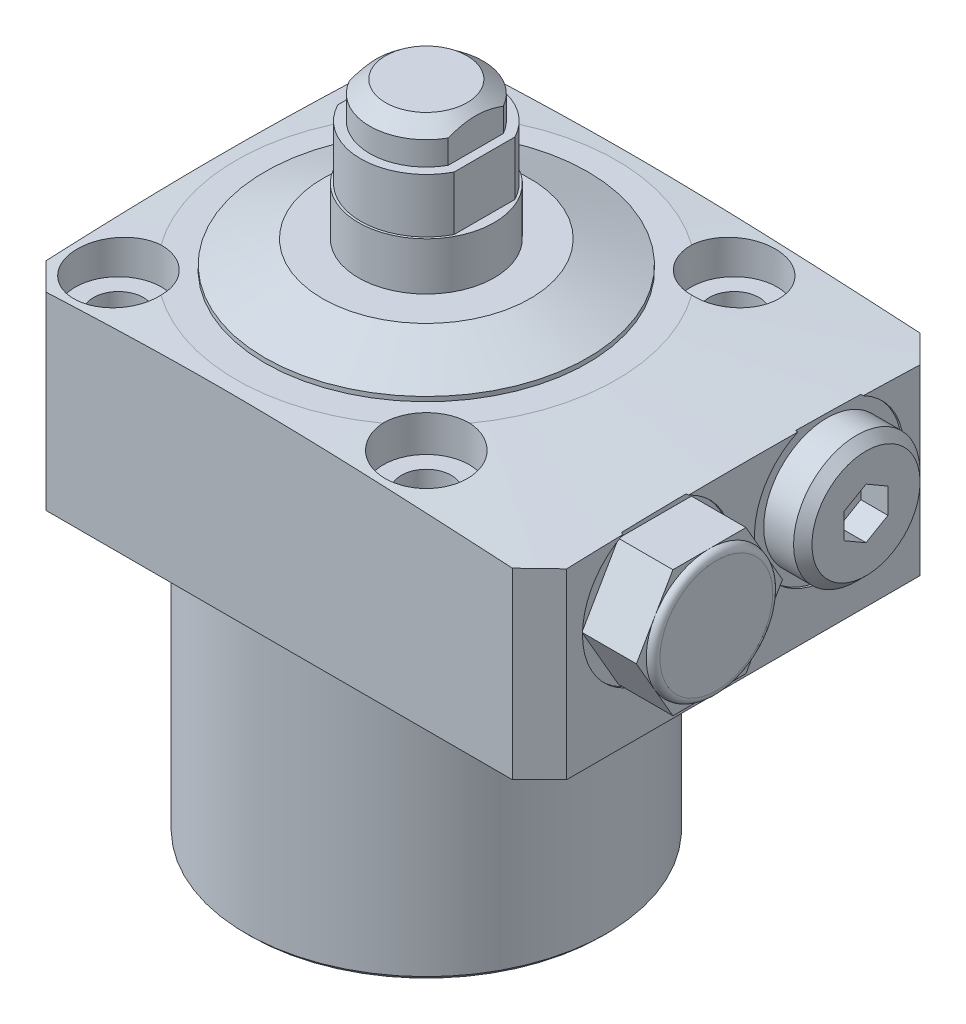
SolidWorks part; units mm, degrees
material "Alloy Steel"
ref_plane "Front Plane" through (0, 0, 0) normal (0, 0, 1) x (1, 0, 0)
ref_plane "Top Plane" through (0, 0, 0) normal (0, 1, 0) x (1, 0, 0)
ref_plane "Right Plane" through (0, 0, 0) normal (1, 0, 0) x (0, 0, -1)
sketch "Sketch1" plane through (0, 0, 0) normal (0, 0, 1) x (1, 0, 0)
  line L0 (0, 0) -> (0, -9.6761) construction
  line L1 (-19.925, 0) -> (-50, 0)
  line L2 (-50, 0) -> (-50, 19.4721)
  line L8 (-19.925, -32.5) -> (-19.925, 0)
  line L9 (-50, 19.4721) -> (-21, 21.5)
  line L10 (-21, 21.5) -> (0, 21.5)
  line L11 (0, 21.5) -> (0, -32.5)
  line L13 (-19.925, -32.5) -> (0, -32.5)
  dimension "D2" = 32.5
  dimension "D3" = 50
  dimension "D7" = 54
  dimension "D8" = 4
  dimension "D9" = 42
  dimension "D10" = 39.85
revolve "Revolve1" add sketch "Sketch1" angle 360 about L0
sketch "Sketch2" plane through (0, 21.5, 0) normal (0, 1, 0) x (1, 0, 0)
  line L0 (0, 0) -> (0, 57.0347) construction
  line L1 (-22.5, 22.5) -> (35, 22.5)
  line L2 (-22.5, 22.5) -> (-22.5, -22.5)
  line L3 (-22.5, -22.5) -> (35, -22.5)
  line L4 (35, 22.5) -> (35, -22.5)
  line L5 (0, 0) -> (-71.4399, 0) construction
  dimension "D1" = 45
  dimension "D2" = 22.5
  dimension "D3" = 57.5
extrude "Cut-Extrude1" cut sketch "Sketch2" against normal through all flip side to cut
chamfer "Chamfer2" distance 3 angle 45 4 edges at (-22.5, 10.3717, -22.5) (35, 10.0295, -22.5) (35, 10.0295, 22.5) (-22.5, 10.3717, 22.5)
sketch "Sketch4" plane through (0, 0, 0) normal (0, 0, 1) x (1, 0, 0)
  line L0 (0, 0) -> (0, 85.9979) construction
  line L1 (0, 39.75) -> (-6.25, 39.75)
  line L2 (-6.25, 39.75) -> (-6.25, 35.762)
  line L3 (-6.25, 35.762) -> (-7.25, 35.762)
  line L4 (-7.25, 35.762) -> (-7.25, 29.782)
  line L5 (-7.25, 29.782) -> (-7.5, 29.782)
  line L6 (-7.5, 29.782) -> (-7.5, 21.5)
  line L7 (21, 21.5) -> (-21, 21.5) construction
  line L8 (-7.5, 21.5) -> (0, 21.5)
  line L9 (0, 21.5) -> (0, 39.75)
  line L12 (32, 0) -> (-19.5, 0) construction
  dimension "D1" = 39.75
  dimension "D2" = 3.988
  dimension "D3" = 12.5
  dimension "D4" = 15
  dimension "D5" = 14.5
  dimension "D6" = 9.968
revolve "Revolve2" add sketch "Sketch4" angle 360 about L0
chamfer "Chamfer1" distance 1.3715 angle 51.98 1 edges at (0, 39.75, -6.25)
sketch "Sketch5" plane through (0, 0, 0) normal (0, 0, 1) x (1, 0, 0)
  line L0 (7.25, 35.762) -> (-7.25, 35.762) construction
  line L1 (-5.46, 35.762) -> (-7.25, 35.762)
  line L2 (-5.46, 35.762) -> (-5.46, 39.75)
  line L3 (-5.46, 39.75) -> (-7.25, 39.75)
  line L4 (-7.25, 35.762) -> (-7.25, 39.75)
  line L5 (4.4959, 39.75) -> (-4.4959, 39.75) construction
  line L6 (-7.25, 35.762) -> (-7.25, 29.782) construction
  line L7 (0, 0) -> (0, 109.405) construction
  line L8 (7.25, 35.762) -> (7.25, 39.75)
  line L9 (5.46, 39.75) -> (7.25, 39.75)
  line L10 (5.46, 35.762) -> (5.46, 39.75)
  line L11 (5.46, 35.762) -> (7.25, 35.762)
  dimension "D1" = 10.92
extrude "Cut-Extrude2" cut sketch "Sketch5" against normal through all and the other way through all
sketch "Sketch6" plane through (0, 0, 0) normal (0, 0, 1) x (1, 0, 0)
  line L0 (7.25, 35.762) -> (-7.25, 35.762) construction
  line L1 (-6.425, 35.762) -> (-7.5, 35.762)
  line L2 (-6.425, 35.762) -> (-6.425, 29.782)
  line L3 (-6.425, 29.782) -> (-7.5, 29.782)
  line L4 (-7.5, 35.762) -> (-7.5, 29.782)
  line L5 (0, 0) -> (0, 83.5625) construction
  line L6 (7.5, 35.762) -> (7.5, 29.782)
  line L7 (6.425, 29.782) -> (7.5, 29.782)
  line L8 (6.425, 35.762) -> (6.425, 29.782)
  line L9 (6.425, 35.762) -> (7.5, 35.762)
  dimension "D1" = 12.85
extrude "Cut-Extrude3" cut sketch "Sketch6" against normal through all and the other way through all
sketch "Sketch10" plane through (0, 21.5, 0) normal (0, 1, 0) x (1, 0, 0)
  line L0 (0, 0) -> (0, 37.6461) construction
  line L1 (0, 0) -> (33.5022, 0) construction
  circle A0 centre (-17, 17) radius 4.75
  dimension "D1" = 9.5
  dimension "D2" = 17
  dimension "D3" = 17
extrude "Cut-Extrude4" cut sketch "Sketch10" against normal offset from surface (4 mm away) 17.5 up to face at (0, 0, 19.925)
hole_wizard "Ø5.5 (5.5) Diameter Hole1" positions "3DSketch1" profile "Sketch11" hole size "Ø5.5" standard "Ansi Metric" end condition through all
sketch3d "3DSketch1"
  circle A0 centre (-17, 17.5, -17) radius 4.75 construction
  point P0 (-17, 17.5, -17)
  point P6 (-17, 22.25, -17)
sketch "Sketch11" plane through (-17, 17.5, -17) normal (1, 0, 0) x (0, 0, 1)
  line L0 (0, 0) -> (0, 50)
  line L1 (0, 50) -> (2.75, 50)
  line L2 (2.75, 50) -> (2.75, 0)
  line L5 (2.75, 0) -> (0, 0)
  line L11 (0, -6.35) -> (0, 107.95) construction
  dimension "Thru Hole Dia." = 5.5
  dimension "Thru Hole Depth" = 50
pattern_circular "CirPattern1" count 4 over 360 about axis through (0, 0, 0) along (0, 1, 0) of "Ø5.5 (5.5) Diameter Hole1", "Cut-Extrude4"
ref_plane "Plane1" through (0, 0, -9.5) normal (0, 0, 1) x (1, 0, 0)
sketch "Sketch12" plane through (0, 0, -9.5) normal (0, 0, 1) x (1, 0, 0)
  line L0 (17.9573, 13) -> (55.5469, 13) construction
  line L2 (35, 21.255) -> (34.75, 21.255)
  line L4 (34.75, 21.255) -> (34.75, 17.953)
  line L5 (34.75, 17.953) -> (34.2166, 17.4196)
  line L6 (34.2166, 17.4196) -> (24.1836, 17.4196)
  line L7 (24.1836, 17.4196) -> (21.528, 13)
  line L8 (21.528, 13) -> (35, 13)
  line L9 (35, 13) -> (35, 21.255)
  line L10 (35, 20.1668) -> (35, 0) construction
  line L11 (-19.925, -32.5) -> (19.925, -32.5) construction
  dimension "D1" = 45.5
  dimension "D2" = 16.51
  dimension "D3" = 0.25
  dimension "D4" = 8.8392
  dimension "D5" = 59
  dimension "D6" = 10.5664
  dimension "D7" = 45
  dimension "D8" = 0.5334
revolve "Cut-Revolve2" cut sketch "Sketch12" angle 360 about L0
sketch "Sketch13" plane through (0, 0, -9.5) normal (0, 0, 1) x (1, 0, 0)
  line L0 (10.4663, 13) -> (36.2703, 13) construction
  line L1 (34.2166, 13) -> (24.1836, 13) construction
  line L3 (34.75, 19.985) -> (38.045, 19.985)
  line L4 (34.75, 4.745) -> (34.75, 20.5019) construction
  line L5 (38.045, 19.985) -> (39.06, 18.97)
  line L6 (39.06, 18.97) -> (39.06, 13)
  line L7 (39.06, 13) -> (34.75, 13)
  line L8 (34.75, 13) -> (34.75, 19.985)
  dimension "D1" = 4.31
  dimension "D2" = 13.97
  dimension "D3" = 45
  dimension "D4" = 1.015
revolve "Revolve3" add sketch "Sketch13" angle 360 about L0
sketch "Sketch14" plane through (39.06, 0, 0) normal (1, 0, 0) x (0, 0, -1)
  line L1 (11.9255, 11.5996) -> (11.9255, 14.4004)
  line L2 (11.9255, 14.4004) -> (9.5, 15.8007)
  line L3 (9.5, 15.8007) -> (7.0745, 14.4004)
  line L4 (7.0745, 14.4004) -> (7.0745, 11.5996)
  line L5 (7.0745, 11.5996) -> (9.5, 10.1993)
  line L6 (9.5, 10.1993) -> (11.9255, 11.5996)
  circle A0 centre (9.5, 13) radius 2.4255 construction
  dimension "D1" = 4.851
extrude "Cut-Extrude5" cut sketch "Sketch14" against normal blind 3
sketch "Sketch16" plane through (9.5, 0, -9.5) normal (0, 0, -1) x (-1, 0, 0)
  line L0 (-17.5, -1.224) -> (-17.5, -24.6754) construction
  line L1 (-17.5, 13.5022) -> (-20, 12)
  line L2 (-20, 12) -> (-20, 2.875)
  line L3 (-20, 2.875) -> (-20.625, 2.25)
  line L4 (-20.625, 2.25) -> (-22.5, 2.25)
  line L5 (-22.5, 2.25) -> (-22.5, 0)
  line L7 (-22.5, 0) -> (-17.5, 0)
  line L8 (-17.5, 0) -> (-17.5, 13.5022)
  line L9 (9.5, -32.5) -> (9.5, 0) construction
  line L10 (29, 0) -> (-22.5, 0) construction
  dimension "D1" = 27
  dimension "D2" = 5
  dimension "D3" = 59
  dimension "D4" = 10
  dimension "D5" = 2.25
  dimension "D6" = 45
  dimension "D7" = 0.625
  dimension "D8" = 9.75
revolve "Cut-Revolve4" cut sketch "Sketch16" angle 360 about L0
pattern_linear "LPattern1" count 2 spacing 19 along (0, 0, 1) of "Cut-Extrude5", "Cut-Revolve2", "Cut-Revolve4"
sketch "Sketch18" plane through (-9.5, 0, -9.5) normal (0, 0, 1) x (1, 0, 0)
  line L0 (36.5, -2.5857) -> (36.5, -21.6782) construction
  line L3 (31.5, 2.25) -> (41.5, 2.25) construction
  line L4 (36.5, 2.875) -> (36.5, 8.5804) construction
  circle A0 centre (33.001, 0.75) radius 1.5
  dimension "D1" = 3
  dimension "D2" = 1.5
  dimension "D3" = 6.998
revolve "Revolve4" add sketch "Sketch18" angle 360 about L0
pattern_linear "LPattern2" count 2 spacing 19 along (0, 0, 1) of bodies 124
chamfer "Chamfer3" distance 0.5 angle 45 1 edges at (0, -32.5, 19.925)
fillet "Fillet1" radius 0.5 1 edges at (0, 0, 19.925)
ref_axis "Axis1" through (0, 29.782, 0) along (0, -1, 0)
sketch "Sketch19" plane through (0, 0, 0) normal (0, 0, 1) x (1, 0, 0)
  line L0 (7.5, 21.5) -> (17.82, 21.5)
  line L1 (21, 21.5) -> (17.0566, 21.5) construction
  line L2 (17.82, 21.5) -> (17.82, 22)
  line L3 (17.82, 22) -> (11.4734, 24.5)
  line L4 (11.4734, 24.5) -> (7.5, 24.5)
  line L5 (7.5, 21.5) -> (7.5, 29.782) construction
  line L6 (7.5, 24.5) -> (7.5, 21.5)
  line L7 (0, 29.782) -> (0, 21.5) construction
  dimension "D1" = 17.82
  dimension "D2" = 21.5
  dimension "D3" = 0.5
  dimension "D4" = 3
revolve "Revolve5" add sketch "Sketch19" angle 360 about axis through (0, 29.782, 0) along (0, -1, 0)
sketch "Sketch20" plane through (34.75, 0, 0) normal (1, 0, 0) x (0, 0, -1)
  line L1 (-1.4344, 13) -> (-5.4672, 19.985)
  line L2 (-5.4672, 19.985) -> (-13.5328, 19.985)
  line L3 (-13.5328, 19.985) -> (-17.5656, 13)
  line L4 (-17.5656, 13) -> (-13.5328, 6.015)
  line L5 (-13.5328, 6.015) -> (-5.4672, 6.015)
  line L6 (-5.4672, 6.015) -> (-1.4344, 13)
  circle A0 centre (-9.5, 13) radius 6.985 construction
  arc A1 (-13.2215, 20.3686) -> (-6.0552, 20.5019) centre (-9.5, 13) ccw
  arc A2 (-13.2215, 20.3686) -> (-6.0552, 20.5019) centre (-9.5, 13) ccw
  spline S1 degree 3 poles (847.6004, -3831.5532) (161.3283, 3919.1103) (-267.8998, -3866.713) (-953.1501, 3822.1882) knots -110.194518 -110.194518 -110.194518 -110.194518 123.34555 123.34555 123.34555 123.34555 only from (-6.0552, 20.5019) to (-13.2215, 20.3686)
  spline S2 degree 3 poles (-6.0552, 20.5019) (-8.4442, 20.4732) (-10.833, 20.428) (-13.2215, 20.3686) knots 0 0 0 0 1 1 1 1
  dimension "D2" = 13.97
  dimension "D1" = 0
extrude "Boss-Extrude2" add sketch "Sketch20" along normal blind 6.78 contours L3 L4 L5 L6 L1 L2
ref_plane "Plane2" through (0, 0, 9.5) normal (0, 0, -1) x (-1, 0, 0)
sketch "Sketch21" plane through (0, 0, 9.5) normal (0, 0, -1) x (-1, 0, 0)
  line L0 (-41.53, 19.985) -> (-41.53, 13) construction
  line L1 (-40.768, 22.9076) -> (-43.889, 22.9076)
  line L2 (-40.768, 22.9076) -> (-40.768, 19.985)
  line L3 (-41.53, 19.223) -> (-43.889, 19.223)
  line L4 (-43.889, 22.9076) -> (-43.889, 19.223)
  line L5 (-41.53, 19.985) -> (-34.75, 19.985) construction
  arc A0 (-40.768, 19.985) -> (-41.53, 19.223) centre (-40.768, 19.223) ccw
  dimension "D1" = 0.762
  dimension "D2" = 0.762
revolve "Cut-Revolve5" cut sketch "Sketch21" angle 360 about axis through (17.9573, 13, 9.5) along (-1, 0, 0)
